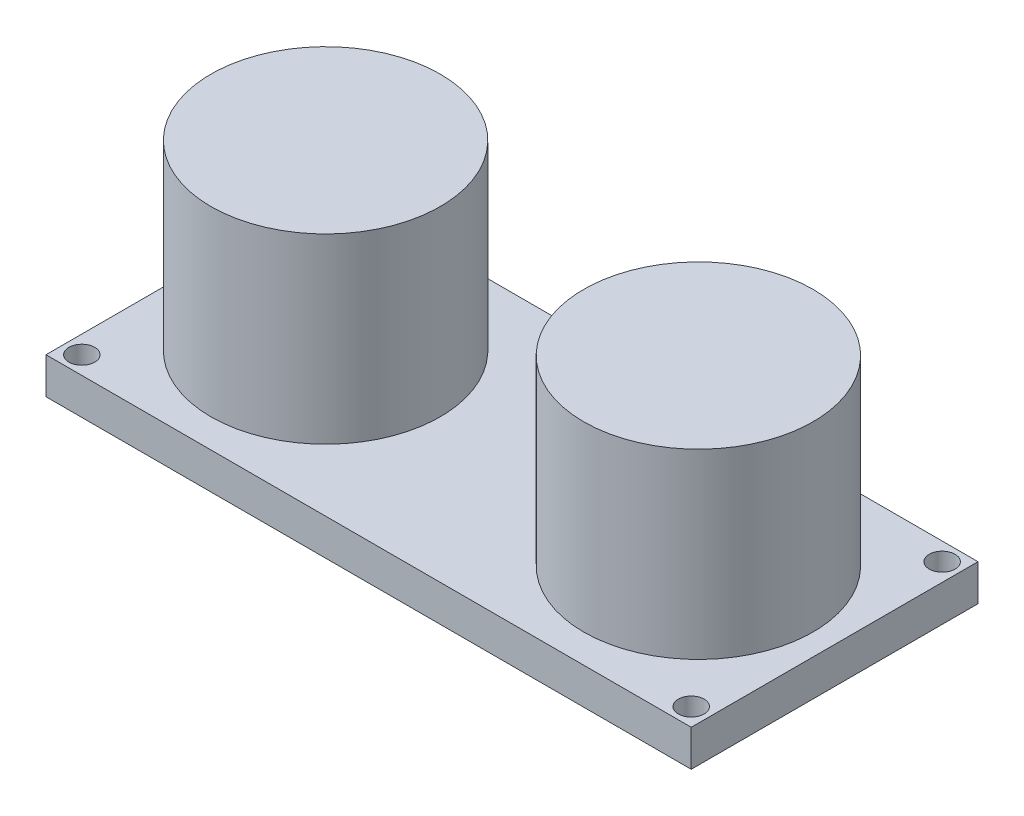
SolidWorks part; units mm, degrees
ref_plane "Front Plane" through (0, 0, 0) normal (0, 0, 1) x (1, 0, 0)
ref_plane "Top Plane" through (0, 0, 0) normal (0, 1, 0) x (1, 0, 0)
ref_plane "Right Plane" through (0, 0, 0) normal (1, 0, 0) x (0, 0, -1)
sketch "Sketch2" plane through (0, 0, 0) normal (0, 1, 0) x (1, 0, 0)
  line L1 (0, 0) -> (45, 0)
  line L2 (0, 0) -> (0, 20)
  line L3 (0, 20) -> (45, 20)
  line L4 (45, 0) -> (45, 20)
  dimension "D1" = 20
  dimension "D2" = 45
extrude "Boss-Extrude1" add sketch "Sketch2" along normal blind 2.54
hole_wizard "M1.6 Clearance Hole1" positions "Sketch4" profile "Sketch5" hole size "M1.6" standard "ANSI Metric" end condition through all
sketch "Sketch4" plane through (0, 2.54, 0) normal (0, 1, 0) x (1, 0, 0)
  line L23 (43.75, 18.75) -> (1.25, 18.75)
  line L24 (1.25, 18.75) -> (1.25, 1.25)
  line L25 (1.25, 1.25) -> (43.75, 1.25)
  line L26 (43.75, 1.25) -> (43.75, 18.75)
  line L31 (1.25, 1.25) -> (0, 1.25) construction
  line L32 (0, 20) -> (0, 0) construction
  line L34 (43.75, 18.75) -> (45, 18.75) construction
  line L35 (45, 0) -> (45, 20) construction
  line L37 (43.75, 18.75) -> (43.75, 20) construction
  line L38 (45, 20) -> (0, 20) construction
  line L40 (1.25, 1.25) -> (1.25, 0) construction
  line L41 (0, 0) -> (45, 0) construction
  point P39 (43.75, 18.75)
  point P40 (1.25, 18.75)
  point P41 (1.25, 1.25)
  point P42 (43.75, 1.25)
  dimension "D2" = 17.5
  dimension "D1" = 42.5
sketch "Sketch5" plane through (43.75, 2.54, -18.75) normal (1, 0, 0) x (0, 0, 1)
  line L0 (0, 0) -> (0, 2.54)
  line L1 (0, 2.54) -> (0.9, 2.54)
  line L2 (0.9, 2.54) -> (0.9, 0)
  line L5 (0.9, 0) -> (0, 0)
  line L11 (0, -6.35) -> (0, 107.95) construction
  dimension "Thru Hole Dia." = 1.8
  dimension "Thru Hole Depth" = 2.54
sketch "Sketch6" plane through (0, 2.54, 0) normal (0, 1, 0) x (1, 0, 0)
  line L0 (9.5, 10) -> (35.5, 10) construction
  line L1 (45, 20) -> (0, 20) construction
  line L3 (0, 20) -> (0, 0) construction
  circle A0 centre (9.5, 10) radius 8
  circle A1 centre (35.5, 10) radius 8
  point P6 (22.5, 20)
  point P7 (22.5, 10)
  point P8 (10.0099, 9.5287)
  point P13 (0, 10)
  dimension "D1" = 16
  dimension "D2" = 26
extrude "Boss-Extrude2" add sketch "Sketch6" along normal blind 12.7
